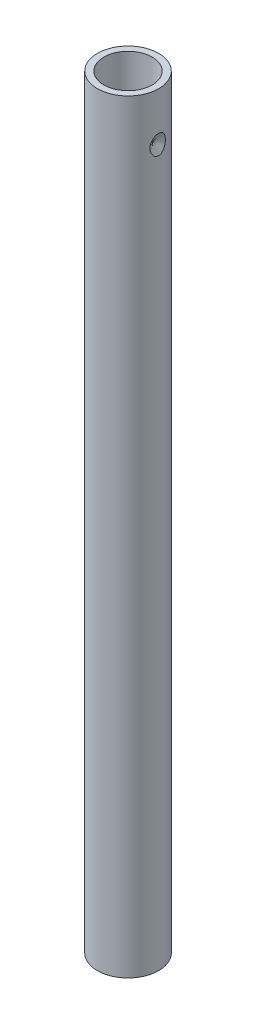
SolidWorks part; units mm, degrees
material "A286 Iron Base Superalloy"
ref_plane "Front Plane" through (0, 0, 0) normal (0, 0, 1) x (1, 0, 0)
ref_plane "Top Plane" through (0, 0, 0) normal (0, 1, 0) x (1, 0, 0)
ref_plane "Right Plane" through (0, 0, 0) normal (1, 0, 0) x (0, 0, -1)
sketch "Sketch1" plane through (0, 0, 0) normal (0, 1, 0) x (1, 0, 0)
  circle A0 centre (0, 0) radius 7.5
  dimension "D1" = 15
extrude "Extrude-Thin1" add sketch "Sketch1" along normal blind 237 thin
sketch "Sketch6" plane through (0, 0, 0) normal (1, 0, 0) x (0, 0, -1)
  line L0 (9.5, 36.8413) -> (9.5, -14.2876) construction
  line L1 (9.5, 0) -> (9.5, 237) construction
  line L5 (0.9024, 8) -> (16.3985, 8) construction
  line L6 (8.5, 8) -> (9.5, 8)
  line L7 (9.5, 8) -> (9.5, 10)
  line L8 (9.5, 10) -> (8.5, 8)
  dimension "D1" = 8
  dimension "D2" = 2
  dimension "D3" = 1
revolve "Cut-Revolve1" cut sketch "Sketch6" angle 360 about L5
sketch3d "3DSketch1" plane through (0, 0, 0) normal (0, 0, 1) x (1, 0, 0)
  dimension "D1" = 9.5
sketch "Sketch7" plane through (0, 0, -9.5) normal (0, 0, 1) x (1, 0, 0)
  circle A0 centre (0, 8) radius 4
  dimension "D1" = 8
sketch "Sketch10" plane through (0, 0, 0) normal (0, 0, 1) x (1, 0, 0)
  line L0 (18.3483, 222) -> (-17.709, 222) construction
  line L1 (9.5, 237) -> (-9.5, 237) construction
  line L2 (9.5, 222) -> (9.5, 225)
  line L4 (9.5, 0) -> (9.5, 237) construction
  line L5 (9.5, 225) -> (8, 222)
  line L6 (8, 222) -> (9.5, 222)
  dimension "D1" = 15
  dimension "D2" = 3
  dimension "D3" = 1.5
revolve "Cut-Revolve3" cut sketch "Sketch10" angle 360 about L0
sketch3d "3DSketch2" plane through (0, 0, 0) normal (0, 0, 1) x (1, 0, 0)
  dimension "D1" = 10
sketch "Sketch11" plane through (10, 0, 0) normal (1, 0, 0) x (0, 0, -1)
  circle A0 centre (0, 222) radius 4
  dimension "D1" = 8
